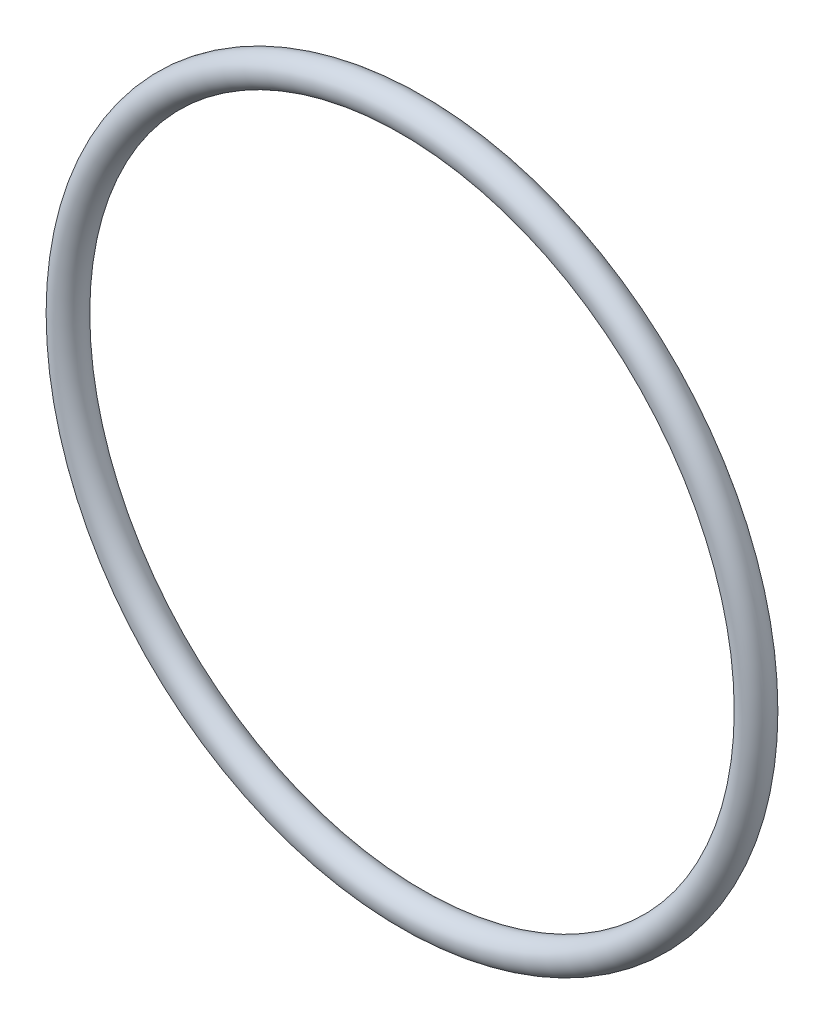
SolidWorks part; units mm, degrees
material "Rubber"
ref_plane "Front" through (0, 0, 0) normal (0, 0, 1) x (1, 0, 0)
ref_plane "Top" through (0, 0, 0) normal (0, 1, 0) x (1, 0, 0)
ref_plane "Right" through (0, 0, 0) normal (1, 0, 0) x (0, 0, -1)
sketch "Sketch1" plane through (0, 0, 0) normal (1, 0, 0) x (0, -1, 0)
  line L0 (0, -0.889) -> (0, 0.889) construction
  line L2 (-24.5034, 0) -> (24.5034, 0) construction
  line L3 (-18.9103, 0) -> (18.9103, 0) construction
  circle A0 centre (19.7993, 0) radius 0.889
  point P9 (18.9103, 0)
  point P10 (20.6883, 0)
  point P13 (19.7993, 0.889)
  point P14 (19.7993, -0.889)
  dimension "Width" = 1.778
  dimension "ID" = 37.8206
revolve "Revolve1" add sketch "Sketch1" angle 360 about L0
